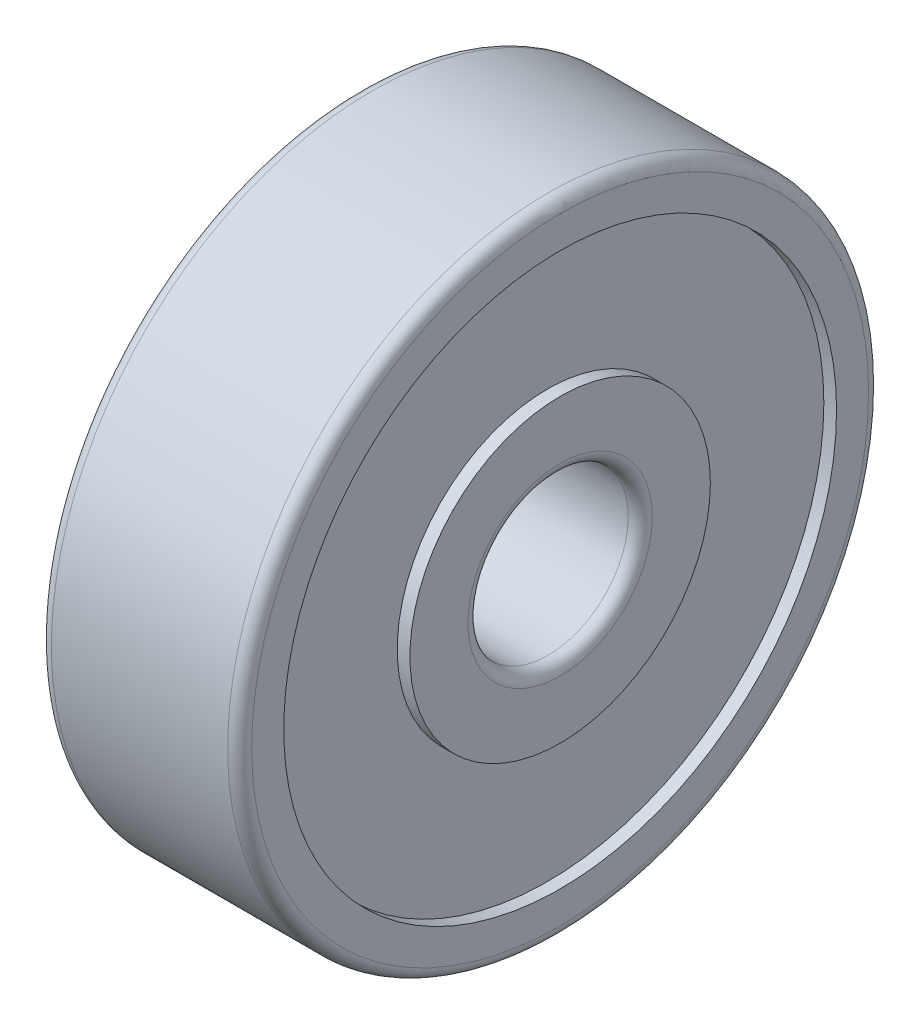
SolidWorks part; units mm, degrees
ref_plane "Front Plane" through (0, 0, 0) normal (0, 0, 1) x (1, 0, 0)
ref_plane "Top Plane" through (0, 0, 0) normal (0, 1, 0) x (1, 0, 0)
ref_plane "Right Plane" through (0, 0, 0) normal (1, 0, 0) x (0, 0, -1)
sketch "Sketch1" plane through (0, 0, 0) normal (0, 0, 1) x (1, 0, 0)
  line L0 (0, 3.75) -> (0, 2.3)
  line L1 (0.3, 2) -> (4.7, 2)
  line L2 (5, 2.3) -> (5, 3.75)
  line L3 (5, 3.75) -> (4.683, 3.75)
  line L4 (4.683, 3.75) -> (4.683, 6.9)
  line L5 (4.683, 6.9) -> (5, 6.9)
  line L6 (5, 6.9) -> (5, 7.7)
  line L7 (4.7, 8) -> (0.3, 8)
  line L8 (0, 7.7) -> (0, 6.9)
  line L9 (0, 6.9) -> (0.317, 6.9)
  line L10 (0.317, 6.9) -> (0.317, 3.75)
  line L11 (0.317, 3.75) -> (0, 3.75)
  line L12 (-0.0014, 0) -> (5.0014, 0) construction
  arc A0 (0, 2.3) -> (0.3, 2) centre (0.3, 2.3) ccw
  arc A1 (4.7, 2) -> (5, 2.3) centre (4.7, 2.3) ccw
  arc A2 (5, 7.7) -> (4.7, 8) centre (4.7, 7.7) ccw
  arc A3 (0.3, 8) -> (0, 7.7) centre (0.3, 7.7) ccw
revolve "Revolve1" add sketch "Sketch1" angle 360 about L12
